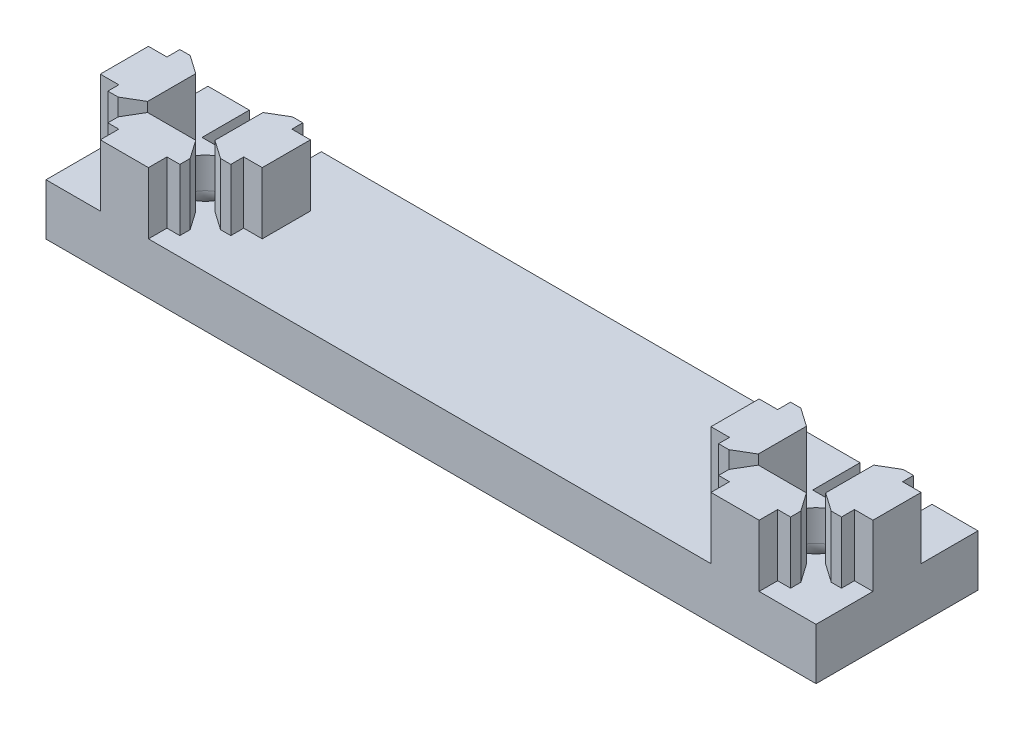
SolidWorks part; units mm, degrees
ref_plane "Front Plane" through (0, 0, 0) normal (0, 0, 1) x (1, 0, 0)
ref_plane "Top Plane" through (0, 0, 0) normal (0, 1, 0) x (1, 0, 0)
ref_plane "Right Plane" through (0, 0, 0) normal (1, 0, 0) x (0, 0, -1)
sketch "Sketch1" plane through (0, 0, 0) normal (0, 1, 0) x (1, 0, 0)
  line L0 (-2.9718, 10) -> (-2.9718, 7.714)
  line L1 (-10, 10) -> (10, 10)
  line L2 (-10, 10) -> (-10, -10)
  line L3 (-10, -10) -> (10, -10)
  line L4 (10, 10) -> (10, -10)
  line L5 (-10, 10) -> (10, -10) construction
  line L6 (-10, -10) -> (10, 10) construction
  line L7 (-2.9718, 10) -> (2.9718, 10) construction
  line L8 (-2.9718, 10) -> (-2.9718, 4.158) construction
  line L9 (-2.9718, 4.158) -> (2.9718, 4.158) construction
  line L10 (2.9718, 10) -> (2.9718, 4.158) construction
  line L11 (-4.5679, 7.714) -> (4.3221, 7.714) construction
  line L12 (-4.5679, 7.714) -> (-4.5679, 6.444) construction
  line L13 (-4.5679, 6.444) -> (4.3221, 6.444) construction
  line L14 (4.3221, 7.714) -> (4.3221, 6.444) construction
  line L15 (-4.5679, 7.714) -> (4.3221, 6.444) construction
  line L16 (-4.5679, 6.444) -> (4.3221, 7.714) construction
  line L17 (-2.9718, 7.714) -> (-4.5679, 7.714)
  line L18 (-4.5679, 7.714) -> (-4.5679, 6.444)
  line L19 (-4.5679, 6.444) -> (-2.9718, 4.158)
  line L20 (-2.9718, 4.158) -> (2.9718, 4.158)
  line L21 (2.9718, 4.158) -> (4.3221, 6.444)
  line L22 (4.3221, 6.444) -> (4.3221, 7.714)
  line L23 (4.3221, 7.714) -> (2.9718, 7.714)
  line L24 (2.9718, 7.714) -> (2.9718, 10)
  line L25 (2.9718, 10) -> (-2.9718, 10)
  line L26 (4.158, -2.9718) -> (4.158, 2.9718)
  line L27 (4.158, 2.9718) -> (6.444, 4.3221)
  line L28 (6.444, 4.3221) -> (7.714, 4.3221)
  line L29 (7.714, 4.3221) -> (7.714, 2.9718)
  line L30 (7.714, 2.9718) -> (10, 2.9718)
  line L31 (10, -2.9718) -> (10, 2.9718) construction
  line L32 (10, 2.9718) -> (10, -2.9718)
  line L33 (10, -2.9718) -> (7.714, -2.9718)
  line L34 (7.714, -2.9718) -> (7.714, -4.5679)
  line L35 (7.714, -4.5679) -> (6.444, -4.5679)
  line L36 (6.444, -4.5679) -> (4.158, -2.9718)
  line L37 (2.9718, -10) -> (-2.9718, -10) construction
  line L38 (4.5679, -6.444) -> (2.9718, -4.158)
  line L39 (4.5679, -7.714) -> (4.5679, -6.444)
  line L40 (2.9718, -7.714) -> (4.5679, -7.714)
  line L41 (2.9718, -10) -> (2.9718, -7.714)
  line L42 (-2.9718, -10) -> (2.9718, -10)
  line L43 (-2.9718, -7.714) -> (-2.9718, -10)
  line L44 (-4.3221, -7.714) -> (-2.9718, -7.714)
  line L45 (-4.3221, -6.444) -> (-4.3221, -7.714)
  line L46 (-2.9718, -4.158) -> (-4.3221, -6.444)
  line L47 (2.9718, -4.158) -> (-2.9718, -4.158)
  line L48 (-10, 2.9718) -> (-10, -2.9718) construction
  line L49 (-10, -2.9718) -> (-10, 2.9718)
  line L50 (-7.714, -2.9718) -> (-10, -2.9718)
  line L51 (-7.714, -4.3221) -> (-7.714, -2.9718)
  line L52 (-6.444, -4.3221) -> (-7.714, -4.3221)
  line L53 (-4.158, -2.9718) -> (-6.444, -4.3221)
  line L54 (-4.158, 2.9718) -> (-4.158, -2.9718)
  line L55 (-6.444, 4.5679) -> (-4.158, 2.9718)
  line L56 (-7.714, 4.5679) -> (-6.444, 4.5679)
  line L57 (-7.714, 2.9718) -> (-7.714, 4.5679)
  line L58 (-10, 2.9718) -> (-7.714, 2.9718)
  point P0 (0, 0)
  point P12 (0, 4.158)
  point P13 (-0.1229, 7.079)
  dimension "D1" = 20
  dimension "D2" = 20
  dimension "D4" = 5.9436
  dimension "D5" = 10
  dimension "D6" = 5.842
  dimension "D7" = 2.286
  dimension "D8" = 3.556
  dimension "D9" = 8.89
extrude "Boss-Extrude1" add sketch "Sketch1" along normal blind 7.62 contours L23 L24 L1 L0 L17 L18 L19 L20 L21 L22 | L26 L27 L28 L29 L30 L32 L33 L34 L35 L36 | L49 L58 L57 L56 L55 L54 L53 L52 L51 L50 | L38 L47 L46 L45 L44 L43 L42 L41 L40 L39
sketch "Sketch2" plane through (0, 0, 0) normal (0, -1, 0) x (1, 0, 0)
  line L1 (10, -10) -> (-122.9538, -10)
  line L2 (10, -10) -> (10, 10)
  line L3 (10, 10) -> (-122.9538, 10)
  line L4 (-122.9538, -10) -> (-122.9538, 10)
  line L5 (10, -10) -> (-122.9538, 10) construction
  line L6 (10, 10) -> (-122.9538, -10) construction
  line L7 (-2.9718, -10) -> (2.9718, -10) construction
  line L8 (10, -2.9718) -> (10, 2.9718) construction
  dimension "D1" = 132.9538
  dimension "D2" = 20
  dimension "D3" = 0
  dimension "D4" = 0
extrude "Boss-Extrude2" add sketch "Sketch2" along normal blind 6.35
pattern_linear "LPattern2" count 2 spacing 75.4126 along (-1, 0, 0) of "Boss-Extrude1"
sketch "Sketch4" plane through (0, -6.35, 0) normal (0, -1, 0) x (-1, 0, 0)
  line L0 (122.9538, 10) -> (122.9538, -0.2108) construction
  line L1 (122.9538, -10) -> (122.9538, 10) construction
  line L2 (122.9538, -10) -> (85.4126, -10)
  line L3 (-10, -10) -> (122.9538, -10) construction
  line L4 (85.4126, -10) -> (122.9538, -0.2108)
  line L5 (122.9538, -0.2108) -> (122.9538, -10)
  dimension "D1" = 10.2108
  dimension "D2" = 37.5412
extrude "Cut-Extrude1" cut sketch "Sketch4" against normal through all
fillet "Fillet1" radius 2.54 1 edges at (-85.4126, -3.175, 10)
sketch "Sketch13" plane through (0, 0, 0) normal (0, 1, 0) x (1, 0, 0)
  line L0 (-79.5706, -2.9718) -> (-81.8566, -4.3221) construction
  line L1 (4.158, 2.9718) -> (-4.158, 2.9718) construction
  line L2 (4.158, 2.9718) -> (4.158, -2.9718) construction
  line L3 (4.158, -2.9718) -> (-4.158, -2.9718) construction
  line L4 (-4.158, 2.9718) -> (-4.158, -2.9718) construction
  line L5 (-71.2546, 2.9718) -> (-79.5706, 2.9718) construction
  line L6 (-71.2546, 2.9718) -> (-71.2546, -2.9718) construction
  line L7 (-71.2546, -2.9718) -> (-79.5706, -2.9718) construction
  line L8 (-79.5706, 2.9718) -> (-79.5706, -2.9718) construction
  line L9 (-79.5706, 2.9718) -> (-79.5706, -2.9718) construction
  line L10 (-75.4126, 2.9718) -> (-75.4126, -2.9718) construction
  circle A0 centre (0, 0) radius 3.5
  circle A1 centre (-75.4126, 0) radius 3.5
  dimension "D1" = 7
  dimension "D2" = 7
extrude "Cut-Extrude5" cut sketch "Sketch13" against normal through all
fillet "Fillet6" radius 2.54 2 edges at (0, -6.35, 3.5) (-75.4126, -6.35, 3.5)
sketch "Sketch14" plane through (0, 7.62, 0) normal (0, 1, 0) x (1, 0, 0)
  line L0 (-78.3844, 4.158) -> (-72.4408, 4.158) construction
  line L5 (4.3221, 10) -> (-4.5679, 10)
  line L6 (4.3221, 10) -> (4.3221, 4.158)
  line L7 (4.3221, 4.158) -> (-4.5679, 4.158)
  line L8 (-4.5679, 10) -> (-4.5679, 4.158)
  line L9 (-71.0905, 4.158) -> (-79.9805, 4.158)
  line L10 (-71.0905, 4.158) -> (-71.0905, 10)
  line L11 (-71.0905, 10) -> (-79.9805, 10)
  line L12 (-79.9805, 4.158) -> (-79.9805, 10)
  line L13 (-71.0905, 4.158) -> (-79.9805, 10) construction
  line L14 (-71.0905, 10) -> (-79.9805, 4.158) construction
  line L15 (-78.3844, 10) -> (-72.4408, 10) construction
  line L16 (-79.9805, 7.714) -> (-79.9805, 6.444) construction
  line L17 (-71.0905, 6.444) -> (-71.0905, 7.714) construction
  line L18 (4.3221, 6.444) -> (4.3221, 7.714) construction
  line L19 (-4.5679, 7.714) -> (-4.5679, 6.444) construction
  point P0 (-75.5355, 7.079)
  point P19 (-79.9805, 7.079)
  dimension "D1" = 0
  dimension "D2" = 0
  dimension "D3" = 0
  dimension "D4" = 0
  dimension "D5" = 0
  dimension "D6" = 0
extrude "Cut-Extrude6" cut sketch "Sketch14" against normal through all
sketch "Sketch15" plane through (-122.9538, 0, 0) normal (-1, 0, 0) x (0, 0, 1)
  line L0 (0.2108, -6.35) -> (-10, -6.35) construction
  line L10 (0.2108, 0) -> (-25.1892, 0)
  line L11 (0.2108, 0) -> (0.2108, -40.894)
  line L12 (0.2108, -40.894) -> (-25.1892, -40.894)
  line L13 (-25.1892, 0) -> (-25.1892, -40.894)
  dimension "D1" = 34.544
  dimension "D2" = 25.4
extrude "Boss-Extrude3" add sketch "Sketch15" against normal blind 12.7
fillet "Fillet15" radius 10.16 1 edges at (-110.2538, -6.35, -4.8946)
fillet "Fillet16" radius 10.16 1 edges at (-110.2538, -8.255, -10)
fillet "Fillet17" radius 10.16 1 edges at (-110.2538, -40.894, -12.4892)
fillet "Fillet18" radius 10.16 4 edges at (-121.6838, -40.894, 0.2108) (-113.2296, -37.9182, 0.2108) (-107.278, -9.3258, 0.2108) (-110.2538, -23.622, 0.2108)
sketch "Sketch18" plane through (-122.9538, 0, 0) normal (-1, 0, 0) x (0, 0, 1)
  line L1 (-25.1892, -40.894) -> (-12.4892, -40.894) construction
  line L2 (-25.1892, -40.894) -> (-25.1892, -28.194) construction
  line L3 (-25.1892, -28.194) -> (-12.4892, -28.194) construction
  line L4 (-12.4892, -40.894) -> (-12.4892, -28.194) construction
  circle A0 centre (-12.4892, -28.194) radius 1.9844
  dimension "D3" = 3.9688
  dimension "D1" = 12.7
  dimension "D2" = 12.7
extrude "Cut-Extrude9" cut sketch "Sketch18" against normal up to surface (12.7 mm away) up to face at (-110.2538, -15.748, -18.4328)
sketch "Sketch19" plane through (0, 0, 0) normal (0, 1, 0) x (1, 0, 0)
  line L1 (-85.0869, -10) -> (-122.9538, -10)
  line L2 (-85.0869, -10) -> (-85.0869, 25.1892)
  line L3 (-85.0869, 25.1892) -> (-122.9538, 25.1892)
  line L4 (-122.9538, -10) -> (-122.9538, 25.1892)
extrude "Cut-Extrude10" cut sketch "Sketch19" against normal through all
